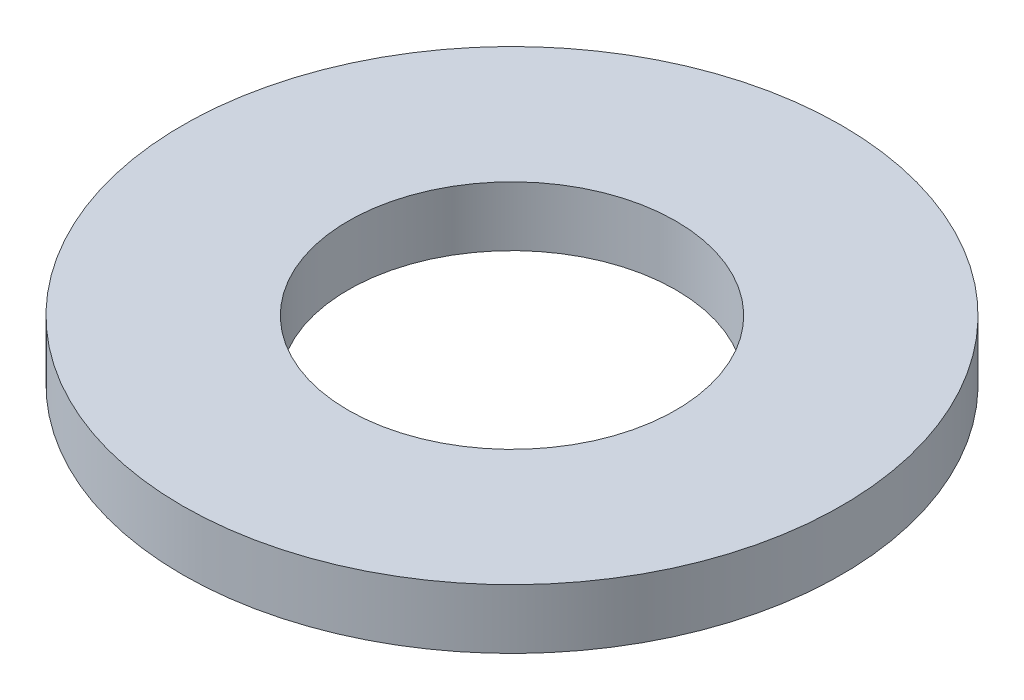
SolidWorks part; units mm, degrees
ref_plane "Front Plane" through (0, 0, 0) normal (0, 0, 1) x (1, 0, 0)
ref_plane "Top Plane" through (0, 0, 0) normal (0, 1, 0) x (1, 0, 0)
ref_plane "Right Plane" through (0, 0, 0) normal (1, 0, 0) x (0, 0, -1)
sketch "Sketch1" plane through (0, 0, 0) normal (0, 1, 0) x (1, 0, 0)
  circle A0 centre (0, 0) radius 2.2
  circle A1 centre (0, 0) radius 4.425
  dimension "D1" = 4.4
  dimension "D2" = 8.85
extrude "Boss-Extrude1" add sketch "Sketch1" along normal blind 0.8
